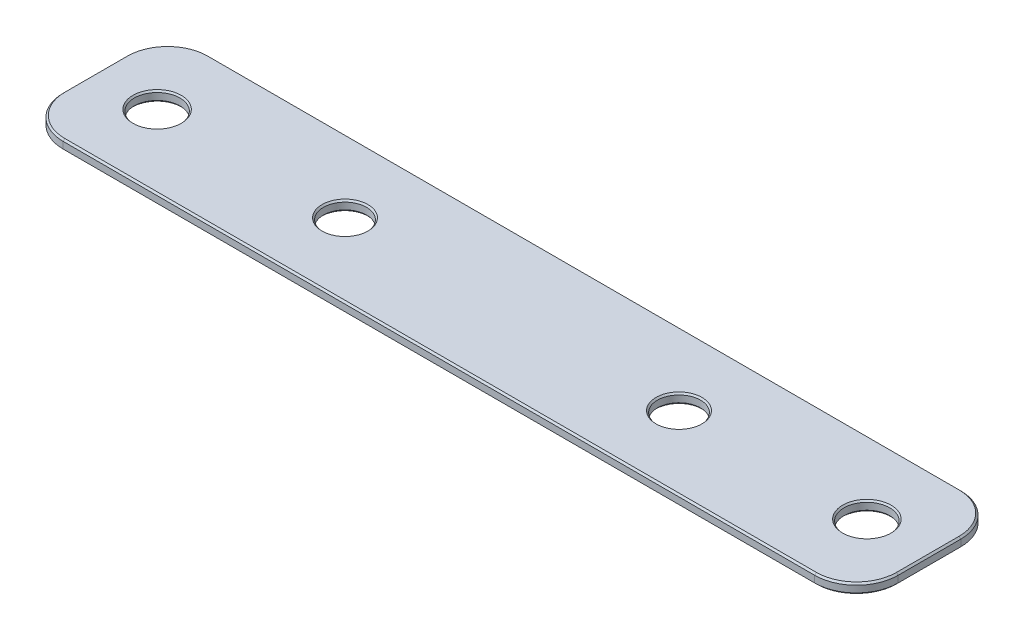
SolidWorks part; units mm, degrees
material "304 SS"
ref_plane "Front Plane" through (0, 0, 0) normal (0, 0, 1) x (1, 0, 0)
ref_plane "Top Plane" through (0, 0, 0) normal (0, 1, 0) x (1, 0, 0)
ref_plane "Right Plane" through (0, 0, 0) normal (1, 0, 0) x (0, 0, -1)
sketch "Sketch1" plane through (0, 0, 0) normal (0, 1, 0) x (1, 0, 0)
  line L0 (-127, -22.225) -> (127, 22.225) construction
  line L1 (-127, 22.225) -> (127, 22.225)
  line L2 (-127, 22.225) -> (-127, -22.225)
  line L3 (-127, -22.225) -> (127, -22.225)
  line L4 (127, 22.225) -> (127, -22.225)
  point P4 (0, 0)
  dimension "D1" = 254
  dimension "D2" = 44.45
extrude "Extrude1" add sketch "Sketch1" along normal blind 3.048
hole_wizard "1/2 Clearance Hole2" positions "Sketch6" profile "Sketch5" hole size "1/2" standard "Ansi Inch"
sketch "Sketch6" plane through (-145.2178, 30.226, 7.1523) normal (0, -1, 0) x (1, 0, 0)
  line L0 (145.2178, -7.1523) -> (132.3707, -7.1523) construction
  line L3 (145.2178, -7.1523) -> (145.2178, 55.4324) construction
  point P0 (196.0178, -7.1523)
  point P19 (94.4178, -7.1523)
  dimension "D1" = 101.6
sketch "Sketch5" plane through (50.8, 30.226, 0) normal (1, 0, 0) x (0, 0, 1)
  line L0 (0, 0) -> (0, 30.226)
  line L1 (0, 30.226) -> (9.525, 30.226)
  line L2 (6.5481, 26.8015) -> (6.5481, 0.5026)
  line L3 (6.5481, 0.5026) -> (6.985, 0)
  line L5 (6.985, 0) -> (0, 0)
  line L6 (-6.5481, 0.5026) -> (-6.985, 0) construction
  line L7 (9.525, 30.226) -> (6.5481, 26.8015)
  line L8 (-9.525, 30.226) -> (-6.5481, 26.8015) construction
  line L11 (0, -6.35) -> (0, 107.95) construction
  dimension "Thru Hole Dia." = 13.0962
  dimension "Thru Hole Depth" = 30.226
  dimension "Near C'Sink Dia." = 13.97
  dimension "Near C'Sink Angle" = 82
  dimension "Far C'Sink Dia." = 19.05
  dimension "Far C'Sink Angle" = 82
hole_wizard "1/2 Clearance Hole1" positions "Sketch4" profile "Sketch3" hole size "1/2" standard "Ansi Inch"
sketch "Sketch4" plane through (-165.1, 30.226, 79.375) normal (0, 1, 0) x (-1, 0, 0)
  line L0 (-57.15, -79.375) -> (-165.1, -79.375) construction
  line L1 (-165.1, -79.375) -> (-273.05, -79.375) construction
  point P0 (-57.15, -79.375)
  point P1 (-273.05, -79.375)
  dimension "D1" = 215.9
sketch "Sketch3" plane through (-107.95, 30.226, 0) normal (1, 0, 0) x (0, 0, 1)
  line L0 (0, 0) -> (0, 30.226)
  line L1 (0, 30.226) -> (9.525, 30.226)
  line L2 (6.9456, 27.2588) -> (6.9456, 0.4836)
  line L3 (6.9456, 0.4836) -> (7.366, 0)
  line L5 (7.366, 0) -> (0, 0)
  line L6 (-6.9456, 0.4836) -> (-7.366, 0) construction
  line L7 (9.525, 30.226) -> (6.9456, 27.2588)
  line L8 (-9.525, 30.226) -> (-6.9456, 27.2588) construction
  line L11 (0, -6.35) -> (0, 107.95) construction
  dimension "Thru Hole Dia." = 13.8913
  dimension "Thru Hole Depth" = 30.226
  dimension "Near C'Sink Dia." = 14.732
  dimension "Near C'Sink Angle" = 82
  dimension "Far C'Sink Dia." = 19.05
  dimension "Far C'Sink Angle" = 82
sketch "Sketch8" [suppressed] plane through (0, 0, 0) normal (0, -1, 0) x (1, 0, 0)
  line L0 (-165.1, -79.375) -> (-165.1, 79.375) construction
  line L1 (-165.1, -31.75) -> (165.1, -31.75)
  line L2 (-165.1, -31.75) -> (-165.1, 31.75)
  line L3 (-165.1, 31.75) -> (165.1, 31.75)
  line L4 (165.1, -31.75) -> (165.1, 31.75)
  line L5 (165.1, 79.375) -> (165.1, -79.375) construction
  point P8 (-165.1, 0)
  dimension "D1" = 63.5
extrude "Extrude3" [suppressed] cut sketch "Sketch8" against normal blind 1.016
fillet "Fillet1" radius 12.7 4 edges at (-127, 1.524, 22.225) (127, 1.524, 22.225) (127, 1.524, -22.225) (-127, 1.524, -22.225)
chamfer "Chamfer1" distance 0.508 angle 45 16 edges at (123.2803, 0, 18.5053) (127, 0, 0) (-127, 0, 0) (-123.2803, 0, 18.5053) (0, 0, 22.225) (-123.2803, 0, -18.5053) (123.2803, 0, -18.5053) (0, 0, -22.225) (0, 3.048, 22.225) (123.2803, 3.048, 18.5053) (-123.2803, 3.048, 18.5053) (127, 3.048, 0) (-127, 3.048, 0) (123.2803, 3.048, -18.5053) (-123.2803, 3.048, -18.5053) (0, 3.048, -22.225)
sketch "Sketch9" plane through (127, 0, 0) normal (1, 0, 0) x (0, 0, -1)
  line L0 (-1.778, 0) -> (1.778, 0)
  line L1 (-9.525, 0) -> (9.525, 0) construction
  arc A0 (-1.778, 0) -> (1.778, 0) centre (0, -6.096) cw
  point P3 (0, 0)
  dimension "D1" = 6.35
  dimension "D2" = 0.254
extrude "Extrude4" cut sketch "Sketch9" against normal through all
hole_wizard "1/2 Clearance Hole4" positions "Sketch11" profile "Sketch10" hole size "1/2" standard "Ansi Inch" end condition through all
sketch "Sketch11" plane through (0, 3.048, 0) normal (0, 1, 0) x (-1, 0, 0)
  line L0 (50.8, 0) -> (-50.8, 0) construction
  point P0 (50.8, 0)
  point P3 (-50.8, 0)
  dimension "D1" = 101.6
sketch "Sketch10" plane through (-50.8, 3.048, 0) normal (1, 0, 0) x (0, 0, 1)
  line L0 (0, 0) -> (0, 3.048)
  line L1 (0, 3.048) -> (6.985, 3.048)
  line L2 (6.5481, 2.5454) -> (6.5481, 0.5026)
  line L3 (6.5481, 0.5026) -> (6.985, 0)
  line L5 (6.985, 0) -> (0, 0)
  line L6 (-6.5481, 0.5026) -> (-6.985, 0) construction
  line L7 (6.985, 3.048) -> (6.5481, 2.5454)
  line L8 (-6.985, 3.048) -> (-6.5481, 2.5454) construction
  line L11 (0, -6.35) -> (0, 107.95) construction
  dimension "Thru Hole Dia." = 13.0962
  dimension "Thru Hole Depth" = 3.048
  dimension "Near C'Sink Dia." = 13.97
  dimension "Near C'Sink Angle" = 82
  dimension "Far C'Sink Dia." = 13.97
  dimension "Far C'Sink Angle" = 82
hole_wizard "1/2 Clearance Hole5" positions "Sketch13" profile "Sketch12" hole size "1/2" standard "Ansi Inch" end condition through all
sketch "Sketch13" plane through (0, 3.048, 0) normal (0, 1, 0) x (-1, 0, 0)
  line L0 (-107.95, 0) -> (107.95, 0) construction
  point P0 (107.95, 0)
  point P1 (-107.95, 0)
  dimension "D1" = 215.9
sketch "Sketch12" plane through (-107.95, 3.048, 0) normal (1, 0, 0) x (0, 0, 1)
  line L0 (0, 0) -> (0, 3.048)
  line L1 (0, 3.048) -> (7.366, 3.048)
  line L2 (6.9456, 2.5644) -> (6.9456, 0.4836)
  line L3 (6.9456, 0.4836) -> (7.366, 0)
  line L5 (7.366, 0) -> (0, 0)
  line L6 (-6.9456, 0.4836) -> (-7.366, 0) construction
  line L7 (7.366, 3.048) -> (6.9456, 2.5644)
  line L8 (-7.366, 3.048) -> (-6.9456, 2.5644) construction
  line L11 (0, -6.35) -> (0, 107.95) construction
  dimension "Thru Hole Dia." = 13.8913
  dimension "Thru Hole Depth" = 3.048
  dimension "Near C'Sink Dia." = 14.732
  dimension "Near C'Sink Angle" = 82
  dimension "Far C'Sink Dia." = 14.732
  dimension "Far C'Sink Angle" = 82
chamfer "Chamfer2" [suppressed] distance 0.508 angle 45
ref_point "Adj Mass Ref Point"
ref_plane "AdvLIGO Front Plane" [suppressed] through (0, 0, 0) normal (0, 0, 1) x (1, 0, 0)
ref_plane "AdvLIGO Top Plane" [suppressed] through (0, 0, 0) normal (0, 1, 0) x (-1, 0, 0)
ref_plane "AdvLIGO Right Plane" [suppressed] through (0, 0, 0) normal (1, 0, 0) x (0, 0, -1)
